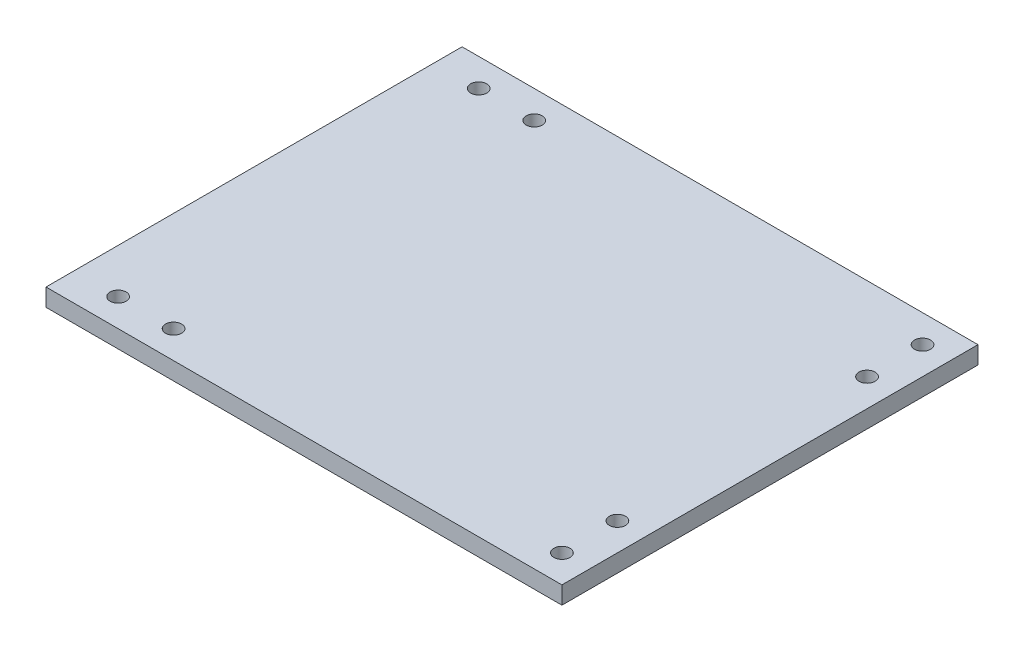
SolidWorks part; units mm, degrees
ref_plane "Front Plane" through (0, 0, 0) normal (0, 0, 1) x (1, 0, 0)
ref_plane "Top Plane" through (0, 0, 0) normal (0, 1, 0) x (1, 0, 0)
ref_plane "Right Plane" through (0, 0, 0) normal (1, 0, 0) x (0, 0, -1)
sketch "Sketch1" plane through (0, 0, 0) normal (0, 1, 0) x (1, 0, 0)
  line L1 (-3, -37.5) -> (90, -37.5)
  line L2 (-3, -37.5) -> (-3, 0)
  line L3 (-3, 0) -> (90, 0)
  line L4 (90, -37.5) -> (90, 0)
  circle A0 centre (85, -32.5) radius 1.45
  circle A1 centre (85, -22.5) radius 1.45
  circle A2 centre (5, -32.5) radius 1.45
  circle A3 centre (15, -32.5) radius 1.45
  dimension "D3" = 2.9
  dimension "D1" = 37.5
  dimension "D2" = 90
  dimension "D4" = 3
  dimension "D5" = 5
  dimension "D6" = 10
  dimension "D7" = 5
  dimension "D8" = 10
  dimension "D9" = 5
extrude "Boss-Extrude1" add sketch "Sketch1" along normal blind 3.175
mirror "Mirror1" about plane through (-3, 3.175, 0) normal (0, 0, 1) of "Boss-Extrude1"
